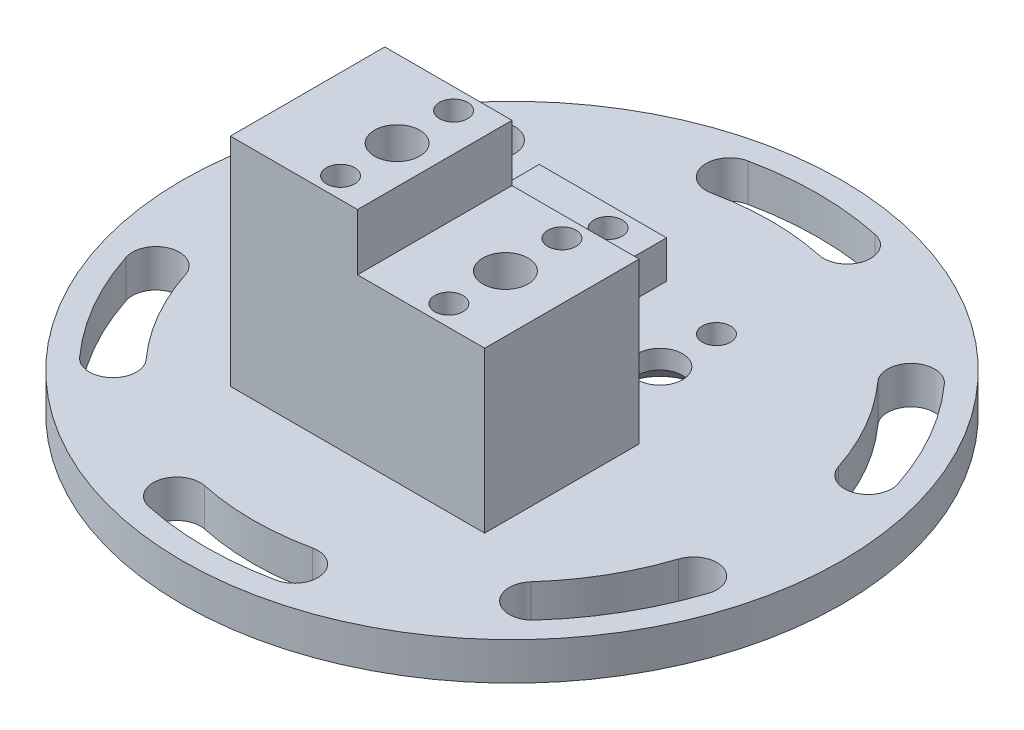
SolidWorks part; units mm, degrees
ref_plane "Front Plane" through (0, 0, 0) normal (0, 0, 1) x (1, 0, 0)
ref_plane "Top Plane" through (0, 0, 0) normal (0, 1, 0) x (1, 0, 0)
ref_plane "Right Plane" through (0, 0, 0) normal (1, 0, 0) x (0, 0, -1)
sketch "Sketch1" plane through (0, 0, 0) normal (0, 1, 0) x (1, 0, 0)
  circle A0 centre (0, 0) radius 17.5
  dimension "D1" = 35
extrude "Boss-Extrude1" add sketch "Sketch1" along normal blind 2
sketch "Sketch2" plane through (0, 2, 0) normal (0, 1, 0) x (1, 0, 0)
  line L0 (0, 0) -> (0, 15) construction
  arc A0 (-3.1187, 14.6722) -> (3.1187, 14.6722) centre (0, 0) cw construction
  arc A1 (3.3786, 15.8949) -> (-3.3786, 15.8949) centre (0, 0) ccw
  arc A2 (2.8588, 13.4495) -> (-2.8588, 13.4495) centre (0, 0) ccw
  arc A3 (2.8588, 13.4495) -> (3.3786, 15.8949) centre (3.1187, 14.6722) ccw
  arc A4 (-3.3786, 15.8949) -> (-2.8588, 13.4495) centre (-3.1187, 14.6722) ccw
  point P4 (0, 15)
  dimension "D3" = 15
  dimension "D1" = 2.5
  dimension "D2" = 24
extrude "Cut-Extrude1" cut sketch "Sketch2" against normal through all
pattern_circular "CirPattern1" count 6 over 360 about axis through (0, 0, 0) along (0, 1, 0) of "Cut-Extrude1"
sketch "Sketch3" plane through (0, 2, 0) normal (0, 1, 0) x (1, 0, 0)
  line L1 (-6.75, -8.2) -> (6.75, -8.2)
  line L2 (-6.75, -8.2) -> (-6.75, 8.2)
  line L3 (-6.75, 8.2) -> (6.75, 8.2)
  line L4 (6.75, -8.2) -> (6.75, 8.2)
  line L5 (-6.75, -8.2) -> (6.75, 8.2) construction
  line L6 (-6.75, 8.2) -> (6.75, -8.2) construction
  point P0 (0, 0)
  dimension "D1" = 13.5
  dimension "D2" = 16.4
extrude "Boss-Extrude2" add sketch "Sketch3" along normal blind 17.5 contours L2 L3 L4 L1
sketch "Sketch4" plane through (0, 19.5, 0) normal (0, 1, 0) x (1, 0, 0)
  line L0 (6.75, -8.2) -> (6.75, 8.2) construction
  line L1 (-6.75, 8.2) -> (6.75, 8.2)
  line L2 (-6.75, 8.2) -> (-6.75, 0)
  line L3 (-6.75, 0) -> (6.75, 0)
  line L4 (6.75, 8.2) -> (6.75, 0)
  dimension "D1" = 8.2
extrude "Cut-Extrude2" cut sketch "Sketch4" against normal blind 11.5
sketch "Sketch5" plane through (0, 0, 8.2) normal (0, 0, 1) x (1, 0, 0)
  line L0 (-6.75, 19.5) -> (-6.75, 13.5)
  line L1 (-6.75, 19.5) -> (6.75, 19.5) construction
  line L2 (-6.75, 13.5) -> (0, 13.5)
  line L3 (0, 13.5) -> (0, 10.5)
  line L4 (0, 10.5) -> (6.75, 10.5)
  line L5 (6.75, 10.5) -> (6.75, 19.5)
  line L9 (6.75, 19.5) -> (-6.75, 19.5)
  line L10 (-6.75, 19.5) -> (-6.75, 2) construction
  dimension "D3" = 6
  dimension "D5" = 6.75
  dimension "D6" = 9
extrude "Cut-Extrude3" cut sketch "Sketch5" against normal through all
sketch "Sketch6" plane through (0, 0, -8.2) normal (0, 0, -1) x (-1, 0, 0)
  line L0 (6.75, 8) -> (6.75, 4)
  line L1 (6.75, 8) -> (-6.75, 8) construction
  line L2 (6.75, 4) -> (0, 4)
  line L3 (0, 4) -> (0, 2)
  line L4 (0, 2) -> (-6.75, 2)
  line L5 (-6.75, 2) -> (-6.75, 8)
  line L9 (-6.75, 8) -> (6.75, 8)
  line L10 (6.75, 8) -> (6.75, 2) construction
  dimension "D2" = 4
  dimension "D3" = 6.75
  dimension "D6" = 6
extrude "Cut-Extrude4" cut sketch "Sketch6" against normal up to surface (8.2 mm away) contours L9 L0 L2 L3 L4 L5 up to face at (0, 10.6667, 0)
hole_wizard "Ø1.5mm Dowel Hole1" positions "Sketch9" profile "Sketch8" hole size "Ø1.5" standard "ISO"
sketch "Sketch9" plane through (0, 13.5, 0) normal (0, 1, 0) x (1, 0, 0)
  line L0 (0, 0) -> (0, -8.2) construction
  point P0 (-2, -1.1)
  point P2 (-2, -7.1)
  point P5 (0, -4.1)
  dimension "D1" = 6
  dimension "D2" = 3
  dimension "D3" = 2
sketch "Sketch8" plane through (-2, 13.5, 1.1) normal (1, 0, 0) x (0, 0, 1)
  line L0 (0, 0) -> (0, 5.4506)
  line L1 (0, 5.4506) -> (0.75, 5)
  line L2 (0.75, 5) -> (0.75, 0)
  line L5 (0.75, 0) -> (0, 0)
  line L10 (0, 5.4506) -> (-0.75, 5) construction
  line L11 (0, -6.35) -> (0, 107.95) construction
  dimension "Hole Dia." = 1.5
  dimension "Hole Depth" = 5
  dimension "Drill Angle" = 118
hole_wizard "Ø1.5mm Dowel Hole2" positions "Sketch11" profile "Sketch10" hole size "Ø1.5" standard "ISO"
sketch "Sketch11" plane through (0, 10.5, 0) normal (0, 1, 0) x (1, 0, 0)
  line L0 (6.75, 0) -> (6.75, -8.2) construction
  point P19 (3.75, -1.1)
  point P21 (3.75, -7.1)
  point P24 (6.75, -4.1)
  dimension "D1" = 6
  dimension "D2" = 3
  dimension "D3" = 3
sketch "Sketch10" plane through (3.75, 10.5, 1.1) normal (1, 0, 0) x (0, 0, 1)
  line L0 (0, 0) -> (0, 3.4506)
  line L1 (0, 3.4506) -> (0.75, 3)
  line L2 (0.75, 3) -> (0.75, 0)
  line L5 (0.75, 0) -> (0, 0)
  line L10 (0, 3.4506) -> (-0.75, 3) construction
  line L11 (0, -6.35) -> (0, 107.95) construction
  dimension "Hole Dia." = 1.5
  dimension "Hole Depth" = 3
  dimension "Drill Angle" = 118
hole_wizard "Ø1.5mm Dowel Hole4" positions "Sketch15" profile "Sketch14" hole size "Ø1.5" standard "ISO"
sketch "Sketch15" plane through (0, 4, 0) normal (0, 1, 0) x (1, 0, 0)
  line L0 (0, 0) -> (0, 8.2) construction
  point P0 (-2, 7.1)
  point P2 (-2, 1.1)
  point P4 (0, 4.1)
  dimension "D1" = 6
  dimension "D2" = 3
  dimension "D3" = 2
sketch "Sketch14" plane through (-2, 4, -7.1) normal (1, 0, 0) x (0, 0, 1)
  line L0 (0, 0) -> (0, 5.4506)
  line L1 (0, 5.4506) -> (0.75, 5)
  line L2 (0.75, 5) -> (0.75, 0)
  line L5 (0.75, 0) -> (0, 0)
  line L10 (0, 5.4506) -> (-0.75, 5) construction
  line L11 (0, -6.35) -> (0, 107.95) construction
  dimension "Hole Dia." = 1.5
  dimension "Hole Depth" = 5
  dimension "Drill Angle" = 118
hole_wizard "Ø1.5mm Dowel Hole3" positions "Sketch13" profile "Sketch12" hole size "Ø1.5" standard "ISO"
sketch "Sketch13" plane through (0, 2, 0) normal (0, 1, 0) x (1, 0, 0)
  line L1 (6.75, -8.2) -> (6.75, 0) construction
  line L2 (0, 0) -> (0, 8.2) construction
  point P15 (3.75, 7.1)
  point P17 (3.75, 1.1)
  point P27 (0, 4.1)
  dimension "D1" = 6
  dimension "D2" = 3
  dimension "D3" = 3
sketch "Sketch12" plane through (3.75, 2, -7.1) normal (1, 0, 0) x (0, 0, 1)
  line L0 (0, 0) -> (0, 5.4506)
  line L1 (0, 5.4506) -> (0.75, 5)
  line L2 (0.75, 5) -> (0.75, 0)
  line L5 (0.75, 0) -> (0, 0)
  line L10 (0, 5.4506) -> (-0.75, 5) construction
  line L11 (0, -6.35) -> (0, 107.95) construction
  dimension "Hole Dia." = 1.5
  dimension "Hole Depth" = 5
  dimension "Drill Angle" = 118
sketch "Sketch16" plane through (0, 13.5, 0) normal (0, 1, 0) x (1, 0, 0)
  line L0 (0, 0) -> (0, -8.2) construction
  line L1 (6.75, 0) -> (6.75, -8.2) construction
  circle A0 centre (-2, -4.1) radius 1
  circle A1 centre (3.75, -4.1) radius 1
  circle A2 centre (3.75, 4.1) radius 1
  circle A3 centre (-2, 4.1) radius 1
  circle A4 centre (-2, 4.1) radius 1
  circle A5 centre (3.75, 7.1) radius 0.75 construction
  circle A6 centre (3.75, -1.1) radius 0.75 construction
  circle A7 centre (3.75, 4.1) radius 1
  circle A8 centre (-2, 7.1) radius 0.75 construction
  dimension "D1" = 2
  dimension "D2" = 3
  dimension "D3" = 3
  dimension "D4" = 3
  dimension "D5" = 2
  dimension "D6" = 3
extrude "Cut-Extrude7" cut sketch "Sketch16" against normal through all contours A0 | A1 | A7 | A4
hole_wizard "CSK for M2 Flat Head Machine Screw2" positions "Sketch23" profile "Sketch22" countersink size "M2" standard "ANSI Metric" end condition through all
sketch "Sketch23" plane through (0, 0, 0) normal (0, -1, 0) x (-1, 0, 0)
  point P0 (-3.75, 4.1)
  point P3 (2, 4.1)
  point P6 (2, -4.1)
  point P9 (-3.75, -4.1)
sketch "Sketch22" plane through (3.75, 0, -4.1) normal (1, 0, 0) x (0, 0, -1)
  line L0 (0, 0) -> (0, 13.5)
  line L1 (0, 13.5) -> (1.2, 13.5)
  line L2 (1.2, 13.5) -> (1.2, 1)
  line L3 (1.2, 1) -> (2.2, 0)
  line L5 (2.2, 0) -> (0, 0)
  line L6 (-1.2, 1) -> (-2.2, 0) construction
  line L11 (0, -6.35) -> (0, 107.95) construction
  dimension "Thru Hole Dia." = 2.4
  dimension "Thru Hole Depth" = 13.5
  dimension "Near C'Sink Dia." = 4.4
  dimension "Near C'Sink Angle" = 90
sketch "Sketch19" plane through (0, 2, 0) normal (0, 1, 0) x (1, 0, 0)
  line L0 (-0.25, 0.75) -> (1.2298, 0.75) construction
  line L1 (-0.25, 1.5) -> (1.2298, 1.5)
  line L2 (-0.25, 0) -> (1.2298, 0)
  line L3 (0, 0) -> (6.75, 0) construction
  line L4 (0, 0) -> (0, 8.2) construction
  arc A0 (-0.25, 1.5) -> (-0.25, 0) centre (-0.25, 0.75) ccw
  arc A1 (1.2298, 0) -> (1.2298, 1.5) centre (1.2298, 0.75) ccw
  point P2 (0.4899, 0.75)
  dimension "D1" = 1.5
  dimension "D2" = 1.4798
  dimension "D3" = 0.25
extrude "Cut-Extrude6" cut sketch "Sketch19" along normal blind 11.5
